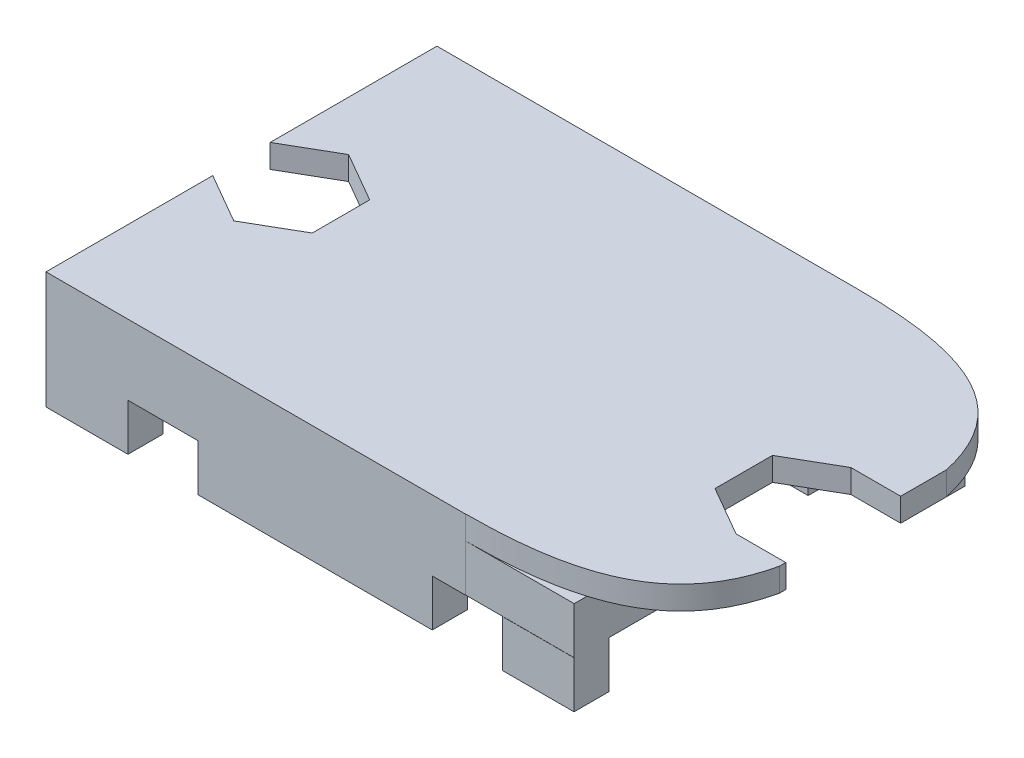
SolidWorks part; units mm, degrees
ref_plane "Front Plane" through (0, 0, 0) normal (0, 0, 1) x (1, 0, 0)
ref_plane "Top Plane" through (0, 0, 0) normal (0, 1, 0) x (1, 0, 0)
ref_plane "Right Plane" through (0, 0, 0) normal (1, 0, 0) x (0, 0, -1)
sketch "Sketch1" plane through (0, 0, 0) normal (0, 1, 0) x (1, 0, 0)
  line L1 (-40.0407, 20.9565) -> (-17.4855, 20.9565)
  line L2 (-40.0407, 20.9565) -> (-40.0407, 8.2565)
  line L3 (-40.0407, 8.2565) -> (-17.4855, 8.2565)
  line L4 (-17.4855, 20.9565) -> (-17.4855, 8.2565)
  dimension "D1" = 22.5552
  dimension "D2" = 12.7
extrude "Boss-Extrude1" add sketch "Sketch1" along normal blind 1
sketch "Sketch2" plane through (0, 1, 0) normal (0, 1, 0) x (1, 0, 0)
  line L0 (-17.4855, 20.9565) -> (-40.0407, 20.9565) construction
  line L1 (-40.0407, 18.2565) -> (-35.0407, 18.2565)
  line L2 (-40.0407, 18.2565) -> (-40.0407, 10.9565)
  line L3 (-40.0407, 10.9565) -> (-35.0407, 10.9565)
  line L4 (-35.0407, 18.2565) -> (-35.0407, 10.9565)
  line L7 (-40.0407, 20.9565) -> (-40.0407, 8.2565) construction
  dimension "D1" = 7.3
  dimension "D2" = 5
  dimension "D3" = 2.7
  dimension "D4" = 0
extrude "Cut-Extrude1" cut sketch "Sketch2" against normal blind 1
sketch "Sketch3" plane through (0, 1, 0) normal (0, 1, 0) x (1, 0, 0)
  line L0 (-17.4855, 8.2565) -> (-17.4855, 20.9565) construction
  line L1 (-17.4855, 16.2565) -> (-22.4855, 16.2565)
  line L2 (-17.4855, 16.2565) -> (-17.4855, 11.2565)
  line L3 (-17.4855, 11.2565) -> (-22.4855, 11.2565)
  line L4 (-22.4855, 16.2565) -> (-22.4855, 11.2565)
  line L5 (-40.0407, 8.2565) -> (-17.4855, 8.2565) construction
  line L6 (-17.4855, 20.9565) -> (-40.0407, 20.9565) construction
  dimension "D1" = 5
  dimension "D2" = 3
  dimension "D3" = 4.7
  dimension "D4" = 5
extrude "Cut-Extrude2" cut sketch "Sketch3" against normal blind 1
sketch "Sketch4" plane through (0, 0, 0) normal (0, -1, 0) x (1, 0, 0)
  line L0 (-17.4855, -8.2565) -> (-17.4855, -11.2565) construction
  line L1 (-40.0407, -8.2565) -> (-17.4855, -8.2565)
  line L2 (-40.0407, -8.2565) -> (-40.0407, -8.7565)
  line L3 (-40.0407, -8.7565) -> (-17.4855, -8.7565)
  line L4 (-17.4855, -8.2565) -> (-17.4855, -8.7565)
  line L5 (-40.0407, -20.9565) -> (-40.0407, -18.2565) construction
  line L6 (-17.4855, -8.2565) -> (-17.9855, -8.2565)
  line L7 (-17.4855, -8.2565) -> (-17.4855, -10.2565)
  line L8 (-17.4855, -10.2565) -> (-17.9855, -10.2565)
  line L9 (-17.9855, -8.2565) -> (-17.9855, -10.2565)
  line L10 (-40.0407, -20.4565) -> (-17.4855, -20.4565)
  line L11 (-40.0407, -20.4565) -> (-40.0407, -20.9565)
  line L12 (-40.0407, -20.9565) -> (-17.4855, -20.9565)
  line L13 (-17.4855, -20.4565) -> (-17.4855, -20.9565)
  line L15 (-17.4855, -20.9565) -> (-17.9855, -20.9565)
  line L16 (-17.4855, -20.9565) -> (-17.4855, -18.4565)
  line L17 (-17.4855, -18.4565) -> (-17.9855, -18.4565)
  line L18 (-17.9855, -20.9565) -> (-17.9855, -18.4565)
  line M3 (-17.4855, -11.2565) -> (-17.4855, -8.2565)
  line M5 (-40.0407, -8.2565) -> (-40.0407, -10.9565)
  line M9 (-40.0407, -18.2565) -> (-40.0407, -20.9565)
  line M10 (-40.0407, -20.9565) -> (-17.4855, -20.9565)
  line M11 (-17.4855, -20.9565) -> (-17.4855, -16.2565)
  dimension "D1" = 0.5
  dimension "D2" = 0.5
  dimension "D3" = 2
  dimension "D4" = 0.5
  dimension "D5" = 2.5
extrude "Boss-Extrude2" add sketch "Sketch4" along normal blind 1 contours L9 L1 L3 M5 | L3 L9 L8 M3 | L18 L10 L17 M11 | L18 L12 L10 M11 | L18 L10 M10 M9
sketch "Sketch5" plane through (0, 1, 0) normal (0, 1, 0) x (1, 0, 0)
  line L0 (-40.0407, 20.9565) -> (-40.0407, 18.2565) construction
  line L1 (-40.0407, 22.9565) -> (-13.4855, 22.9565)
  line L2 (-40.0407, 22.9565) -> (-40.0407, 6.2565)
  line L3 (-40.0407, 6.2565) -> (-13.4855, 6.2565)
  line L4 (-13.4855, 22.9565) -> (-13.4855, 6.2565)
  line L5 (-17.4855, 20.9565) -> (-40.0407, 20.9565) construction
  line L6 (-40.0407, 8.2565) -> (-17.4855, 8.2565) construction
  line L7 (-17.4855, 16.2565) -> (-17.4855, 20.9565) construction
  dimension "D1" = 0
  dimension "D2" = 2
  dimension "D3" = 2
  dimension "D4" = 4
extrude "Boss-Extrude3" add sketch "Sketch5" along normal blind 1
sketch "Sketch6" plane through (0, 2, 0) normal (0, 1, 0) x (1, 0, 0)
  line L1 (-40.0407, 13.3797) -> (-37.9157, 12.1528)
  line L2 (-37.9157, 12.1528) -> (-35.7907, 13.3797)
  line L3 (-35.7907, 13.3797) -> (-35.7907, 15.8334)
  line L4 (-35.7907, 15.8334) -> (-37.9157, 17.0603)
  line L5 (-37.9157, 17.0603) -> (-40.0407, 15.8334)
  line L6 (-40.0407, 15.8334) -> (-40.0407, 13.3797)
  line L7 (-40.0407, 22.9565) -> (-40.0407, 6.2565) construction
  line L8 (-40.0407, 6.2565) -> (-13.4855, 6.2565) construction
  circle A0 centre (-37.9157, 14.6065) radius 2.125 construction
  dimension "D1" = 4.25
  dimension "D2" = 2.125
  dimension "D3" = 8.35
extrude "Cut-Extrude3" cut sketch "Sketch6" against normal blind 1
sketch "Sketch7" plane through (0, 1, 0) normal (0, -1, 0) x (-1, 0, 0)
  line L0 (13.4855, 6.2565) -> (13.4855, 22.9565) construction
  line L1 (17.7355, 14.9834) -> (15.6105, 16.2103)
  line L2 (15.6105, 16.2103) -> (13.4855, 14.9834)
  line L3 (13.4855, 14.9834) -> (13.4855, 12.5297)
  line L4 (13.4855, 12.5297) -> (15.6105, 11.3028)
  line L5 (15.6105, 11.3028) -> (17.7355, 12.5297)
  line L6 (17.7355, 12.5297) -> (17.7355, 14.9834)
  circle A0 centre (15.6105, 13.7565) radius 2.125 construction
  dimension "D1" = 4.25
  dimension "D2" = 0
extrude "Cut-Extrude4" cut sketch "Sketch7" against normal blind 1
sketch "Sketch8" plane through (0, 2, 0) normal (0, 1, 0) x (1, 0, 0)
  line L0 (-13.4855, 22.9565) -> (-40.0407, 22.9565) construction
  line L1 (-13.4855, 14.9834) -> (-13.4855, 22.9565) construction
  spline S0 degree 3 poles (-22.1278, 22.9565) (-17.368, 22.9565) (-14.3027, 21.872) (-13.4855, 18.1762) knots 0 0 0 0 1 1 1 1
extrude "Cut-Extrude5" cut sketch "Sketch8" along direction (0, 1, 0) on the side against the normal through all and the other way through all
sketch "Sketch9" plane through (0, 2, 0) normal (0, 1, 0) x (1, 0, 0)
  line L0 (-22.1278, 22.9565) -> (-40.0407, 22.9565) construction
  line L1 (-40.0407, 6.2565) -> (-13.4855, 6.2565) construction
  point P0 (-32.2929, 14.6065)
  dimension "D1" = 8.35
  dimension "D2" = 8.35
ref_plane "Plane1" through (0, 0, -14.61) normal (0, 0, 1) x (1, 0, 0)
mirror "Mirror2" about plane through (0, 0, -14.61) normal (0, 0, 1) of "Cut-Extrude5"
sketch "Sketch10" plane through (0, 1, 0) normal (0, -1, 0) x (-1, 0, 0)
  line L0 (40.0407, 8.2565) -> (17.4855, 8.2565) construction
  line L1 (40.0407, 6.2565) -> (17.4855, 6.2565)
  line L2 (40.0407, 6.2565) -> (40.0407, 8.2565)
  line L3 (40.0407, 8.2565) -> (17.4855, 8.2565)
  line L4 (17.4855, 6.2565) -> (17.4855, 8.2565)
  line L5 (40.0407, 20.9565) -> (17.4855, 20.9565) construction
  line L6 (40.0407, 22.9565) -> (17.4855, 22.9565)
  line L7 (40.0407, 22.9565) -> (40.0407, 20.9565)
  line L8 (40.0407, 20.9565) -> (17.4855, 20.9565)
  line L9 (17.4855, 22.9565) -> (17.4855, 20.9565)
  line L10 (17.4855, 8.2565) -> (17.4855, 11.2565) construction
  line L11 (17.4855, 16.2565) -> (17.4855, 20.9565) construction
  dimension "D1" = 0
  dimension "D2" = 0
extrude "Boss-Extrude4" add sketch "Sketch10" along normal blind 2
sketch "Sketch11" plane through (0, 2, 0) normal (0, 1, 0) x (1, 0, 0)
  line L1 (-22.1278, 6.2635) -> (-13.2079, 6.2635)
  line L2 (-22.1278, 6.2635) -> (-22.1278, 5.533)
  line L3 (-22.1278, 5.533) -> (-13.2079, 5.533)
  line L4 (-13.2079, 6.2635) -> (-13.2079, 5.533)
extrude "Cut-Extrude6" cut sketch "Sketch11" against normal blind 3
sketch "Sketch12" plane through (0, -1, 0) normal (0, -1, 0) x (-1, 0, 0)
  line L0 (17.4855, 10.2565) -> (17.4855, 6.2635) construction
  line L1 (40.0407, 6.2565) -> (17.4855, 6.2565)
  line L2 (40.0407, 6.2565) -> (40.0407, 7.7565)
  line L3 (40.0407, 7.7565) -> (17.4855, 7.7565)
  line L4 (17.4855, 6.2565) -> (17.4855, 7.7565)
  line L5 (17.4855, 22.4089) -> (17.4855, 16.2565) construction
  line L6 (40.0407, 22.9565) -> (17.4855, 22.9565)
  line L7 (40.0407, 22.9565) -> (40.0407, 21.4565)
  line L8 (40.0407, 21.4565) -> (17.4855, 21.4565)
  line L9 (17.4855, 22.9565) -> (17.4855, 21.4565)
  dimension "D1" = 1.5
  dimension "D2" = 1.5
extrude "Boss-Extrude5" add sketch "Sketch12" along normal blind 2
sketch "Sketch13" plane through (0, -3, 0) normal (0, -1, 0) x (-1, 0, 0)
  line L0 (17.4855, 6.2565) -> (40.0407, 6.2565) construction
  line L1 (36.5407, 6.2565) -> (33.5407, 6.2565)
  line L2 (36.5407, 6.2565) -> (36.5407, 7.7565)
  line L3 (36.5407, 7.7565) -> (33.5407, 7.7565)
  line L4 (33.5407, 6.2565) -> (33.5407, 7.7565)
  line L5 (40.0407, 7.7565) -> (17.4855, 7.7565) construction
  line L6 (17.4855, 21.4565) -> (40.0407, 21.4565) construction
  line L7 (36.5407, 21.4565) -> (33.5407, 21.4565)
  line L8 (36.5407, 21.4565) -> (36.5407, 22.9565)
  line L9 (36.5407, 22.9565) -> (33.5407, 22.9565)
  line L10 (33.5407, 21.4565) -> (33.5407, 22.9565)
  line L11 (40.0407, 22.9565) -> (17.4855, 22.9565) construction
  line L12 (40.0407, 6.2565) -> (40.0407, 7.7565) construction
  line L13 (23.5407, 6.2565) -> (23.5407, 7.7565)
  line L14 (23.5407, 6.2565) -> (20.5407, 6.2565)
  line L15 (20.5407, 6.2565) -> (20.5407, 7.7565)
  line L16 (23.5407, 7.7565) -> (20.5407, 7.7565)
  line L17 (23.5407, 21.4565) -> (23.5407, 22.9565)
  line L18 (23.5407, 21.4565) -> (20.5407, 21.4565)
  line L19 (20.5407, 21.4565) -> (20.5407, 22.9565)
  line L20 (23.5407, 22.9565) -> (20.5407, 22.9565)
  line L21 (17.4855, 7.7565) -> (17.4855, 6.2565) construction
  dimension "D1" = 3
  dimension "D2" = 3.5
  dimension "D3" = 0
  dimension "D4" = 3
  dimension "D6" = 3.0552
  dimension "D5" = 2
extrude "Cut-Extrude7" cut sketch "Sketch13" against normal blind 2
sketch "Sketch14" plane through (0, 2, 0) normal (0, 1, 0) x (1, 0, 0)
  line L1 (-15.6105, 16.2103) -> (-13.4855, 16.2103)
  line L2 (-15.6105, 16.2103) -> (-15.6105, 14.9834)
  line L3 (-15.6105, 14.9834) -> (-13.4855, 14.9834)
  line L4 (-13.4855, 16.2103) -> (-13.4855, 14.9834)
  line L5 (-15.6105, 11.3028) -> (-13.4855, 11.3028)
  line L6 (-15.6105, 11.3028) -> (-15.6105, 12.5297)
  line L7 (-15.6105, 12.5297) -> (-13.4855, 12.5297)
  line L8 (-13.4855, 11.3028) -> (-13.4855, 12.5297)
extrude "Cut-Extrude8" cut sketch "Sketch14" against normal blind 1
